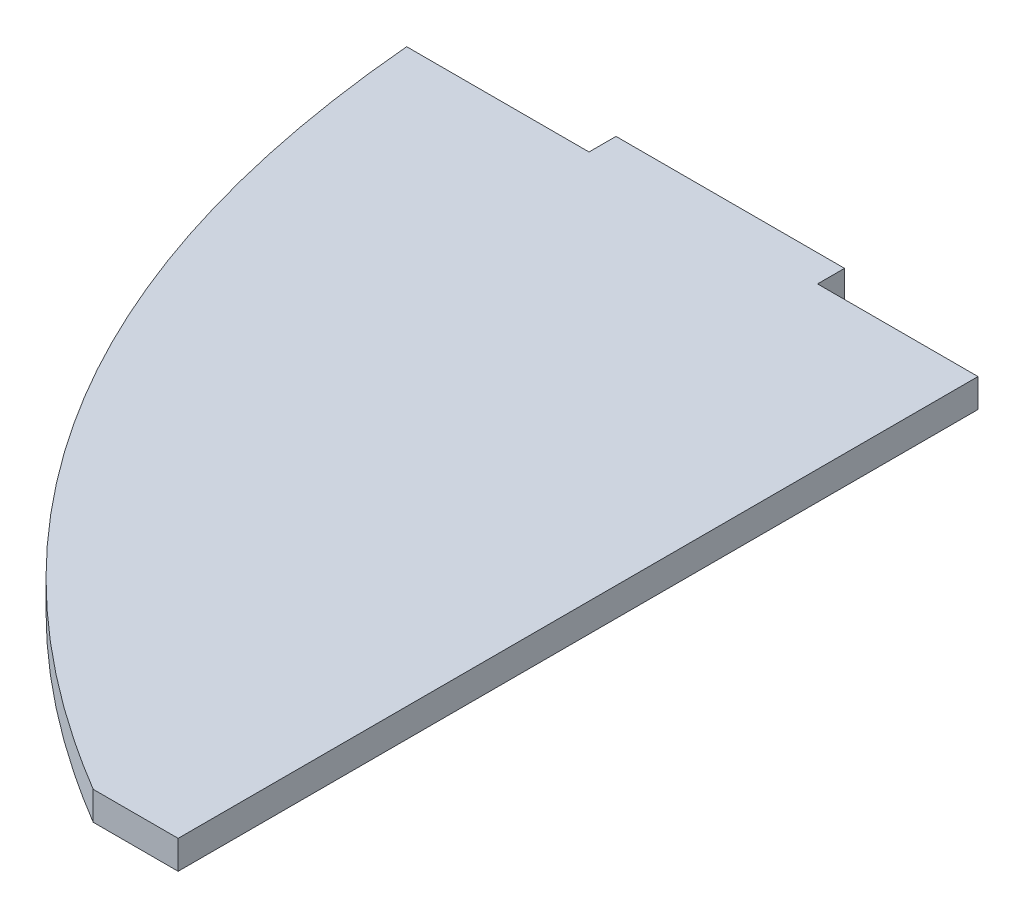
SolidWorks part; units mm, degrees
ref_plane "Front Plane" through (0, 0, 0) normal (0, 0, 1) x (1, 0, 0)
ref_plane "Top Plane" through (0, 0, 0) normal (0, 1, 0) x (1, 0, 0)
ref_plane "Right Plane" through (0, 0, 0) normal (1, 0, 0) x (0, 0, -1)
sketch "Sketch1" plane through (0, 0, 0) normal (0, 1, 0) x (1, 0, 0)
  line L0 (36.7862, 0) -> (18.9532, 0)
  line L1 (36.7862, 0) -> (36.7862, -88.9)
  line L2 (27.3468, -88.9) -> (36.7862, -88.9)
  line L6 (-6.4468, 0) -> (-6.4468, 3)
  line L7 (-6.4468, 3) -> (18.9532, 3)
  line L8 (18.9532, 3) -> (18.9532, 0)
  line L9 (-6.4468, 0) -> (-26.7138, 0)
  spline S0 degree 2 poles (27.3468, -88.9) (-21.535, -59.7712) (-26.7138, 0) knots 0 0 0 1 1 1
  dimension "D1" = 63.5
  dimension "D2" = 88.9
  dimension "D3" = 25.4
  dimension "D4" = 3
extrude "Boss-Extrude1" add sketch "Sketch1" against normal blind 3.175
